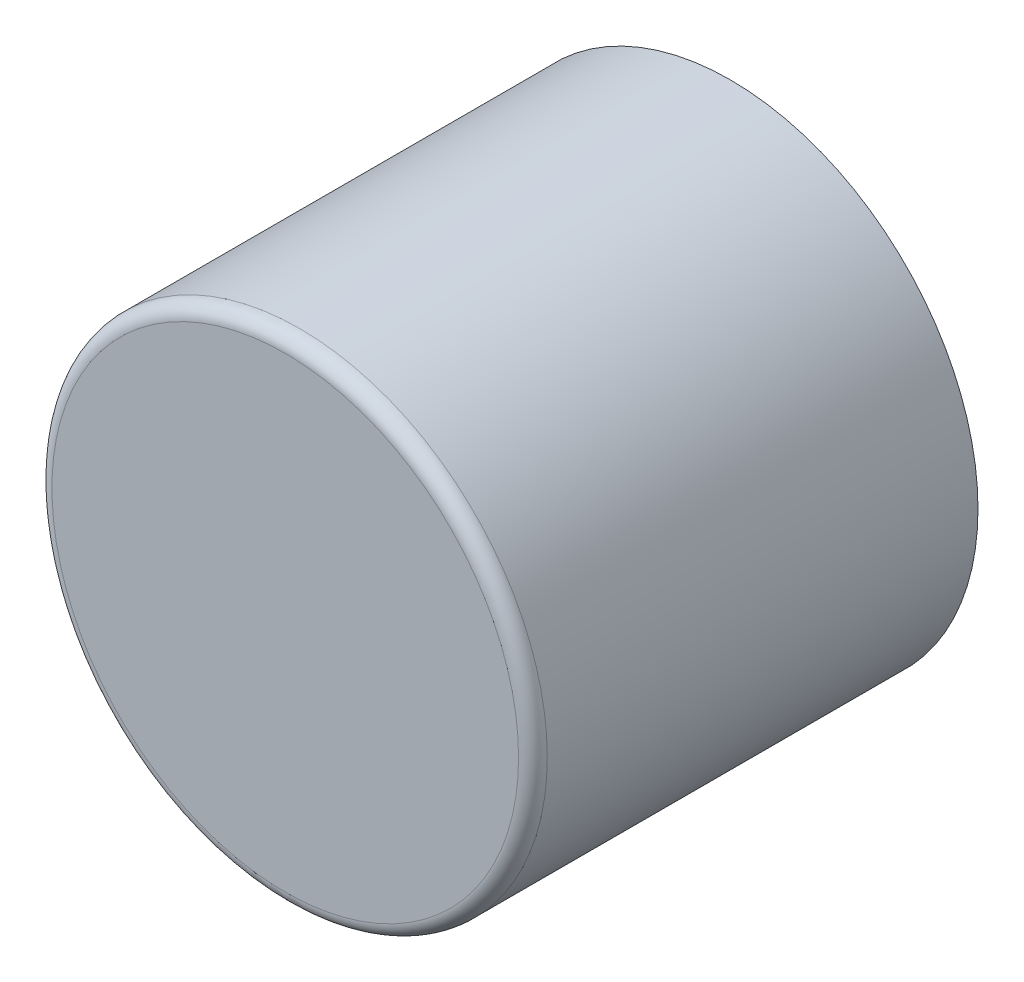
SolidWorks part; units mm, degrees
ref_plane "Front Plane" through (0, 0, 0) normal (0, 0, 1) x (1, 0, 0)
ref_plane "Top Plane" through (0, 0, 0) normal (0, 1, 0) x (1, 0, 0)
ref_plane "Right Plane" through (0, 0, 0) normal (1, 0, 0) x (0, 0, -1)
sketch "Sketch1" plane through (0, 0, 0) normal (0, 0, 1) x (1, 0, 0)
  circle A0 centre (0, 0) radius 17.25
  dimension "D1" = 34.5
extrude "Boss-Extrude1" add sketch "Sketch1" along normal blind 31
fillet "Fillet1" radius 1 1 edges at (17.25, 0, 31)
